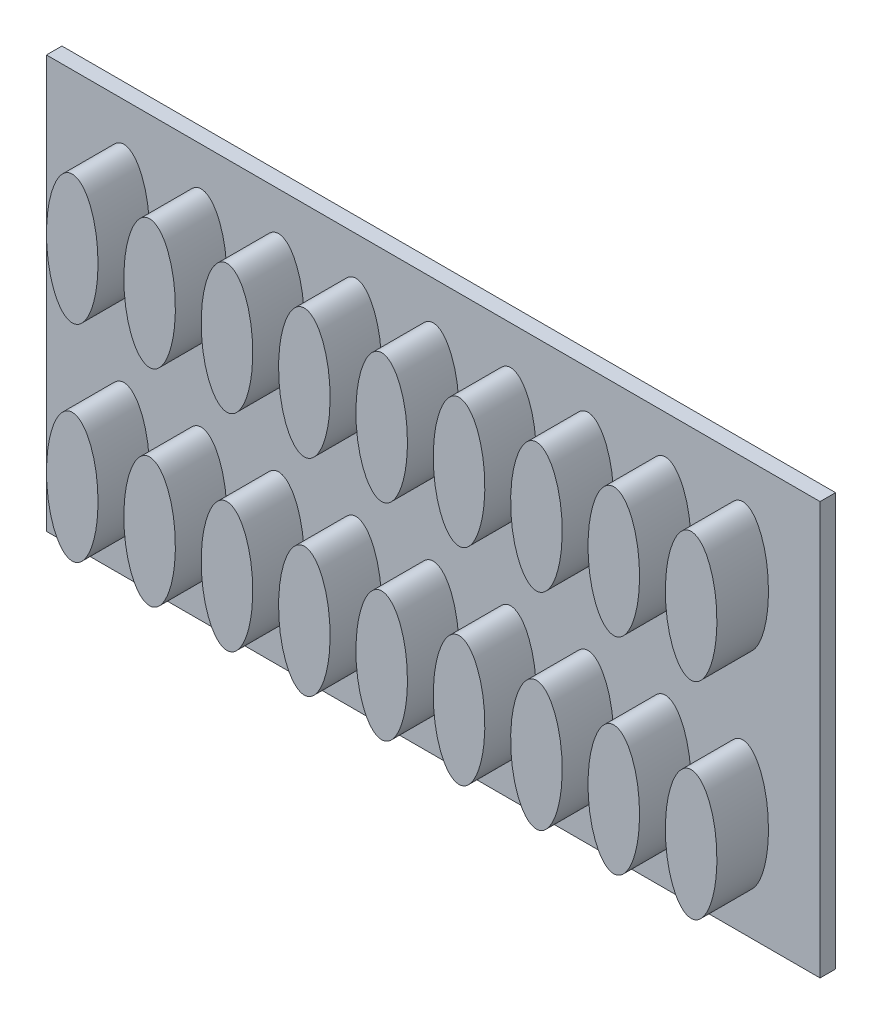
SolidWorks part; units mm, degrees
ref_plane "Přední rovina" through (0, 0, 0) normal (0, 0, 1) x (1, 0, 0)
ref_plane "Horní rovina" through (0, 0, 0) normal (0, 1, 0) x (1, 0, 0)
ref_plane "Pravá rovina" through (0, 0, 0) normal (1, 0, 0) x (0, 0, -1)
sketch "Skica1" plane through (0, 0, 0) normal (0, 0, 1) x (1, 0, 0)
  line L1 (0, 0) -> (150, 0)
  line L2 (0, 0) -> (0, 80)
  line L3 (0, 80) -> (150, 80)
  line L4 (150, 0) -> (150, 80)
  dimension "D1" = 150
  dimension "D2" = 80
extrude "Vysunout1" add sketch "Skica1" along normal blind 3
sketch "Skica2" plane through (0, 0, 3) normal (0, 0, 1) x (1, 0, 0)
  line L0 (0, 80) -> (0, 0) construction
  line L1 (150, 80) -> (0, 80) construction
  ellipse E0 centre (15, 60) end of major axis (15, 72.5) minor radius 5
  dimension "D1" = 10
  dimension "D2" = 25
  dimension "D3" = 15
  dimension "D4" = 20
extrude "Vysunout2" add sketch "Skica2" along normal blind 10
pattern_linear "LinPole1" count 9 spacing 15 along (-1, 0, 0) count 2 spacing 40 along (0, -1, 0) of "Vysunout2"
